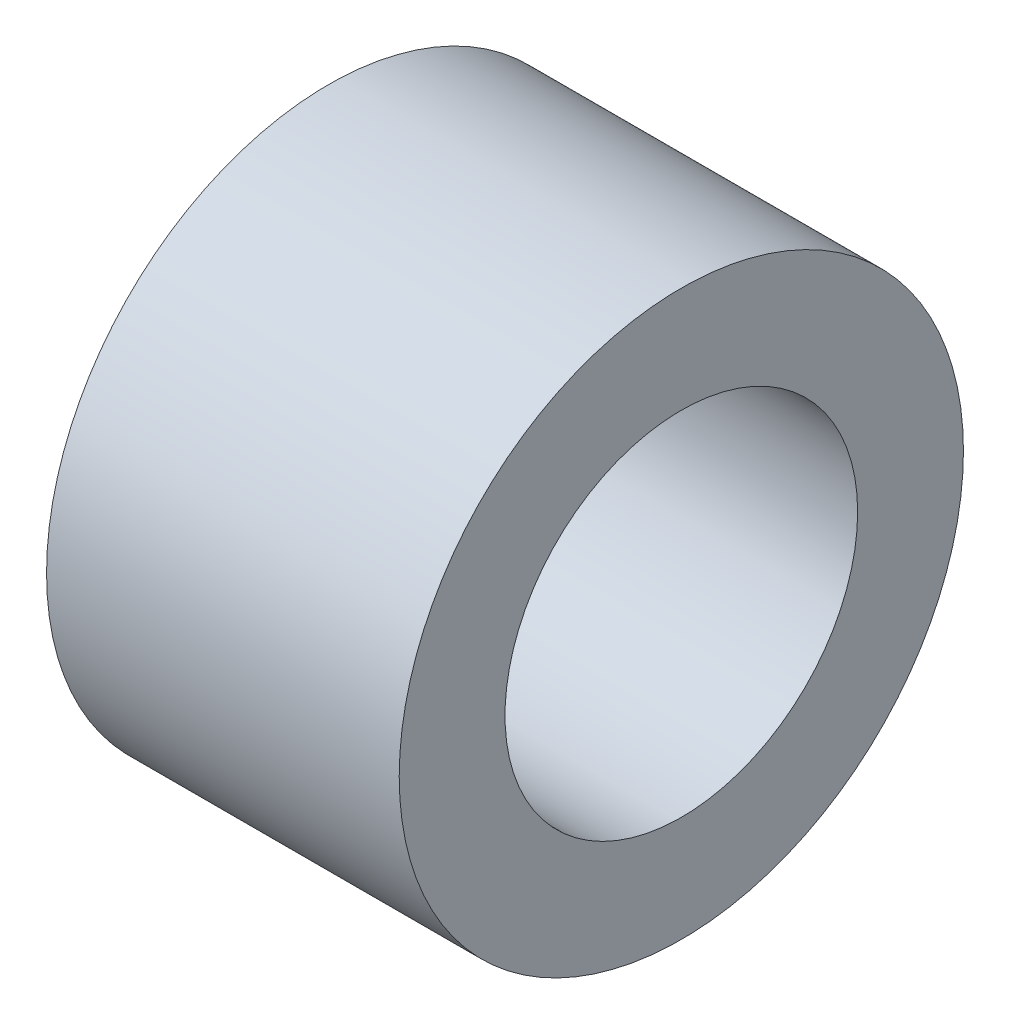
SolidWorks part; units mm, degrees
ref_plane "Front Plane" through (0, 0, 0) normal (0, 0, 1) x (1, 0, 0)
ref_plane "Top Plane" through (0, 0, 0) normal (0, 1, 0) x (1, 0, 0)
ref_plane "Right Plane" through (0, 0, 0) normal (1, 0, 0) x (0, 0, -1)
sketch "Sketch1" plane through (0, 0, 0) normal (1, 0, 0) x (0, 0, -1)
  circle A0 centre (0, 0) radius 3.81
extrude "Boss-Extrude1" add sketch "Sketch1" along normal blind 4.7625
sketch "Sketch2" plane through (4.7625, 0, 0) normal (1, 0, 0) x (0, 0, -1)
  circle A0 centre (0, 0) radius 2.3813
extrude "Cut-Extrude1" cut sketch "Sketch2" against normal through all
